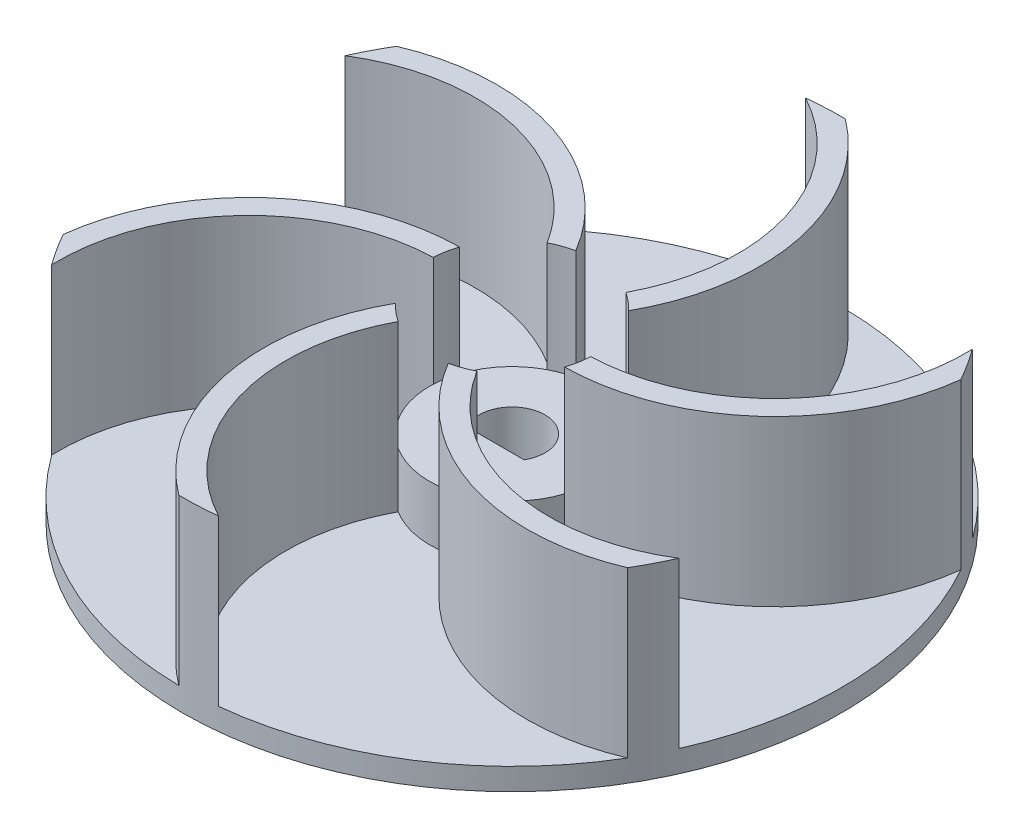
SolidWorks part; units mm, degrees
ref_plane "Front Plane" through (0, 0, 0) normal (0, 0, 1) x (1, 0, 0)
ref_plane "Top Plane" through (0, 0, 0) normal (0, 1, 0) x (1, 0, 0)
ref_plane "Right Plane" through (0, 0, 0) normal (1, 0, 0) x (0, 0, -1)
sketch "Sketch1" plane through (0, 0, 0) normal (0, 1, 0) x (1, 0, 0)
  circle A0 centre (0, 0) radius 30
  dimension "D1" = 60
extrude "Boss-Extrude1" add sketch "Sketch1" along normal blind 2
sketch "Sketch2" plane through (0, 0, 0) normal (0, 1, 0) x (1, 0, 0)
  circle A0 centre (0, 0) radius 7.5
  dimension "D1" = 15
extrude "Boss-Extrude2" add sketch "Sketch2" along normal blind 7
sketch "Sketch3" plane through (0, 2, 0) normal (0, 1, 0) x (1, 0, 0)
  circle A0 centre (0, 0) radius 7.4461
  circle A1 centre (0, 0) radius 30
  arc A2 (0, 0) -> (-34.3356, 6.2987) centre (-18.2133, -2.5499) ccw
  arc A3 (0.9903, 0.1386) -> (-35.2122, 6.7798) centre (-18.2133, -2.5499) ccw
  arc A4 (-0.9903, -0.1386) -> (-33.4589, 5.8175) centre (-18.2133, -2.5499) ccw
  circle M2 centre (0, 0) radius 7.5
  circle M3 centre (0, 0) radius 30
  dimension "D1" = 1
  dimension "D2" = 1
extrude "Boss-Extrude3" add sketch "Sketch3" along normal blind 15 contours A4 A2 M2 M3 | A3 A1 A2 M2
sketch "Sketch4" plane through (0, 0, 0) normal (0, 1, 0) x (1, 0, 0)
  line L0 (-2.5981, -1.5) -> (2.5981, -1.5)
  arc A0 (2.5981, -1.5) -> (-2.5981, -1.5) centre (0, 0) ccw
  dimension "D1" = 6
  dimension "D2" = 1.5
extrude "Cut-Extrude1" cut sketch "Sketch4" along normal through all
pattern_circular "CirPattern2" count 6 over 360 about axis through (0, 0, 0) along (0, 1, 0) of "Boss-Extrude3"
